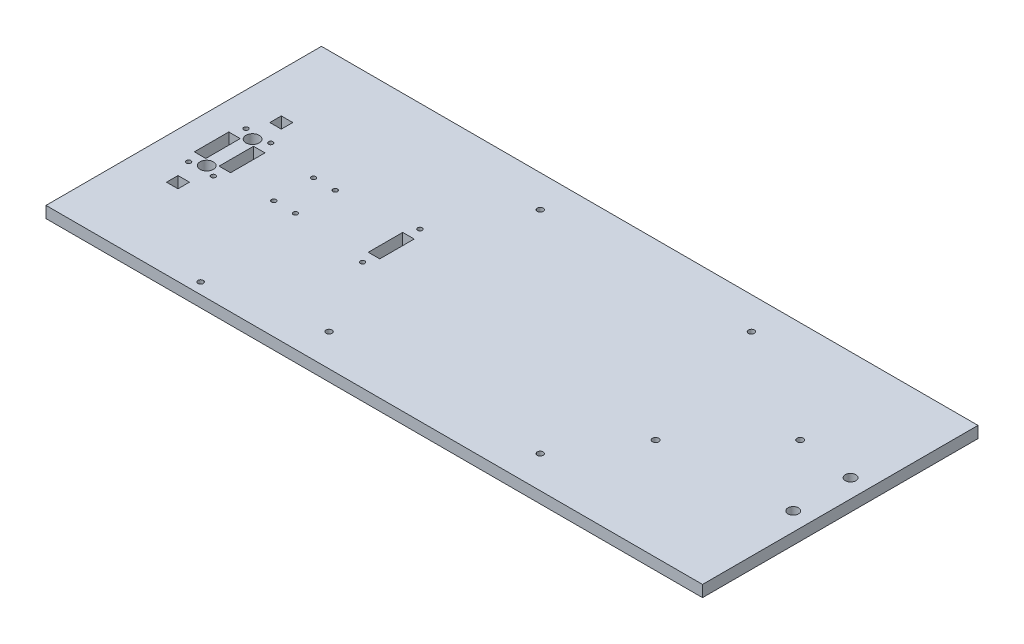
SolidWorks part; units mm, degrees
ref_plane "Front Plane" through (0, 0, 0) normal (0, 0, 1) x (1, 0, 0)
ref_plane "Top Plane" through (0, 0, 0) normal (0, 1, 0) x (1, 0, 0)
ref_plane "Right Plane" through (0, 0, 0) normal (1, 0, 0) x (0, 0, -1)
sketch "Sketch1" plane through (0, 0, 0) normal (0, 1, 0) x (1, 0, 0)
  line L0 (25.4, 88.9) -> (25.4, 63.5) construction
  line L1 (0, 0) -> (363.22, 0)
  line L2 (0, 0) -> (0, 152.4)
  line L3 (0, 152.4) -> (363.22, 152.4)
  line L4 (363.22, 0) -> (363.22, 152.4)
  line L5 (353.06, 92.075) -> (353.06, 60.325) construction
  line L6 (353.06, 76.2) -> (25.4, 76.2) construction
  line L7 (25.4, 76.2) -> (0, 76.2) construction
  line L8 (353.06, 76.2) -> (363.22, 76.2) construction
  circle A0 centre (25.4, 63.5) radius 3.6703
  circle A1 centre (25.4, 88.9) radius 3.6703
  circle A2 centre (353.06, 60.325) radius 2.921
  circle A3 centre (353.06, 92.075) radius 2.921
  dimension "D3" = 5.842
  dimension "D7" = 7.3406
  dimension "D1" = 152.4
  dimension "D2" = 10.16
  dimension "D4" = 327.66
  dimension "D5" = 25.4
  dimension "D6" = 31.75
  dimension "D8" = 25.4
extrude "Boss-Extrude1" add sketch "Sketch1" along normal blind 6.35
sketch "Sketch2" plane through (0, 6.35, 0) normal (0, 1, 0) x (1, 0, 0)
  line L0 (25.4, 88.9) -> (25.4, 101.6) construction
  line L1 (28.575, 101.6) -> (22.225, 101.6)
  line L2 (28.575, 101.6) -> (28.575, 107.95)
  line L3 (28.575, 107.95) -> (22.225, 107.95)
  line L4 (22.225, 101.6) -> (22.225, 107.95)
  line L5 (22.225, 50.8) -> (28.575, 50.8)
  line L6 (22.225, 50.8) -> (22.225, 44.45)
  line L7 (22.225, 44.45) -> (28.575, 44.45)
  line L8 (28.575, 50.8) -> (28.575, 44.45)
  line L9 (25.4, 63.5) -> (25.4, 50.8) construction
  line L10 (18.5547, 85.725) -> (18.5547, 104.775) construction
  line L11 (29.0703, 85.725) -> (35.4203, 85.725)
  line L12 (29.0703, 85.725) -> (29.0703, 66.675)
  line L13 (29.0703, 66.675) -> (35.4203, 66.675)
  line L14 (35.4203, 85.725) -> (35.4203, 66.675)
  line L15 (15.3797, 85.725) -> (21.7297, 85.725)
  line L16 (15.3797, 85.725) -> (15.3797, 66.675)
  line L17 (15.3797, 66.675) -> (21.7297, 66.675)
  line L18 (21.7297, 85.725) -> (21.7297, 66.675)
  line L19 (18.5547, 104.775) -> (22.225, 104.775) construction
  line L20 (28.575, 104.775) -> (32.2453, 104.775) construction
  line L21 (32.2453, 104.775) -> (32.2453, 85.725) construction
  line L22 (32.2453, 66.675) -> (32.2453, 47.625) construction
  line L23 (32.2453, 47.625) -> (28.575, 47.625) construction
  line L24 (18.5547, 66.675) -> (18.5547, 47.625) construction
  line L25 (18.5547, 47.625) -> (22.225, 47.625) construction
  line L27 (111.6203, 85.725) -> (117.9703, 85.725)
  line L28 (111.6203, 85.725) -> (111.6203, 66.675)
  line L29 (111.6203, 66.675) -> (117.9703, 66.675)
  line L30 (117.9703, 85.725) -> (117.9703, 66.675)
  circle A0 centre (25.4, 88.9) radius 3.6703 construction
  dimension "D1" = 12.7
  dimension "D2" = 6.35
  dimension "D3" = 6.35
  dimension "D5" = 19.05
  dimension "D6" = 6.35
  dimension "D7" = 76.2
extrude "Cut-Extrude1" cut sketch "Sketch2" against normal through all
sketch "Sketch5" plane through (0, 6.35, 0) normal (0, 1, 0) x (1, 0, 0)
  line L2 (79.4639, 6.096) -> (79.4639, 0) construction
  line L3 (79.4639, 6.096) -> (0, 6.096) construction
  line L6 (0, 152.4) -> (0, 0) construction
  line L7 (0, 0) -> (363.22, 0) construction
  circle A1 centre (79.4639, 6.096) radius 1.5
  dimension "D1" = 3
  dimension "D2" = 79.4639
  dimension "D3" = 6.096
extrude "Cut-Extrude2" cut sketch "Sketch5" against normal through all contours A1
sketch "Sketch7" plane through (0, 6.35, 0) normal (0, 1, 0) x (1, 0, 0)
  line L0 (138.8079, 76.2) -> (0, 76.2) construction
  line L1 (138.8079, 134.62) -> (255.6479, 134.62) construction
  line L2 (138.8079, 134.62) -> (138.8079, 17.78) construction
  line L3 (138.8079, 17.78) -> (255.6479, 17.78) construction
  line L4 (255.6479, 134.62) -> (255.6479, 17.78) construction
  line L5 (0, 152.4) -> (0, 0) construction
  circle A0 centre (138.8079, 134.62) radius 1.651
  circle A1 centre (255.6479, 134.62) radius 1.651
  circle A2 centre (255.6479, 17.78) radius 1.651
  circle A3 centre (138.8079, 17.78) radius 1.651
  dimension "D2" = 3.302
  dimension "D1" = 116.84
extrude "Cut-Extrude3" cut sketch "Sketch7" against normal through all
sketch "Sketch8" plane through (0, 6.35, 0) normal (0, 1, 0) x (1, 0, 0)
  line L0 (321.0479, 76.2) -> (363.22, 76.2) construction
  line L1 (281.0479, 96.2) -> (321.0479, 96.2) construction
  line L2 (281.0479, 96.2) -> (281.0479, 56.2) construction
  line L3 (281.0479, 56.2) -> (321.0479, 56.2) construction
  line L4 (321.0479, 96.2) -> (321.0479, 56.2) construction
  line L5 (363.22, 0) -> (363.22, 152.4) construction
  circle A0 centre (281.0479, 96.2) radius 1.75 construction
  circle A1 centre (321.0479, 96.2) radius 1.75
  circle A2 centre (321.0479, 56.2) radius 1.75 construction
  circle A3 centre (281.0479, 56.2) radius 1.75
  circle A4 centre (255.6479, 134.62) radius 1.651 construction
  dimension "D2" = 3.5
  dimension "D1" = 40
  dimension "D3" = 25.4
extrude "Cut-Extrude4" cut sketch "Sketch8" against normal through all
sketch "Sketch9" plane through (0, 6.35, 0) normal (0, 1, 0) x (1, 0, 0)
  line L0 (18.5547, 85.725) -> (18.5547, 92.075) construction
  line L1 (21.7297, 85.725) -> (15.3797, 85.725) construction
  line L2 (32.2453, 85.725) -> (32.2453, 92.075) construction
  line L3 (35.4203, 85.725) -> (29.0703, 85.725) construction
  line L4 (32.2453, 66.675) -> (32.2453, 60.325) construction
  line L5 (29.0703, 66.675) -> (35.4203, 66.675) construction
  line L6 (18.5547, 66.675) -> (18.5547, 60.325) construction
  line L7 (15.3797, 66.675) -> (21.7297, 66.675) construction
  line L8 (114.7953, 92.075) -> (114.7953, 85.725) construction
  line L9 (117.9703, 85.725) -> (111.6203, 85.725) construction
  line L10 (114.7953, 60.325) -> (114.7953, 66.675) construction
  line L11 (111.6203, 66.675) -> (117.9703, 66.675) construction
  circle A0 centre (18.5547, 92.075) radius 1.25
  circle A1 centre (32.2453, 92.075) radius 1.25
  circle A2 centre (32.2453, 60.325) radius 1.25
  circle A3 centre (18.5547, 60.325) radius 1.25
  circle A4 centre (114.7953, 92.075) radius 1.25
  circle A5 centre (114.7953, 60.325) radius 1.25
  dimension "D1" = 2.5
  dimension "D2" = 6.35
extrude "Cut-Extrude5" cut sketch "Sketch9" against normal through all
sketch "Sketch10" plane through (0, 6.35, 0) normal (0, 1, 0) x (1, 0, 0)
  line L0 (60.8203, 76.2) -> (35.4203, 76.2) construction
  line L1 (60.8203, 87.2) -> (72.8203, 87.2) construction
  line L2 (60.8203, 87.2) -> (60.8203, 65.2) construction
  line L3 (60.8203, 65.2) -> (72.8203, 65.2) construction
  line L4 (72.8203, 87.2) -> (72.8203, 65.2) construction
  line L5 (35.4203, 66.675) -> (35.4203, 85.725) construction
  circle A0 centre (60.8203, 87.2) radius 1.25
  circle A1 centre (72.8203, 87.2) radius 1.25
  circle A2 centre (72.8203, 65.2) radius 1.25
  circle A3 centre (60.8203, 65.2) radius 1.25
  dimension "D1" = 2.5
  dimension "D2" = 12
  dimension "D3" = 22
  dimension "D4" = 25.4
extrude "Cut-Extrude6" cut sketch "Sketch10" against normal through all
